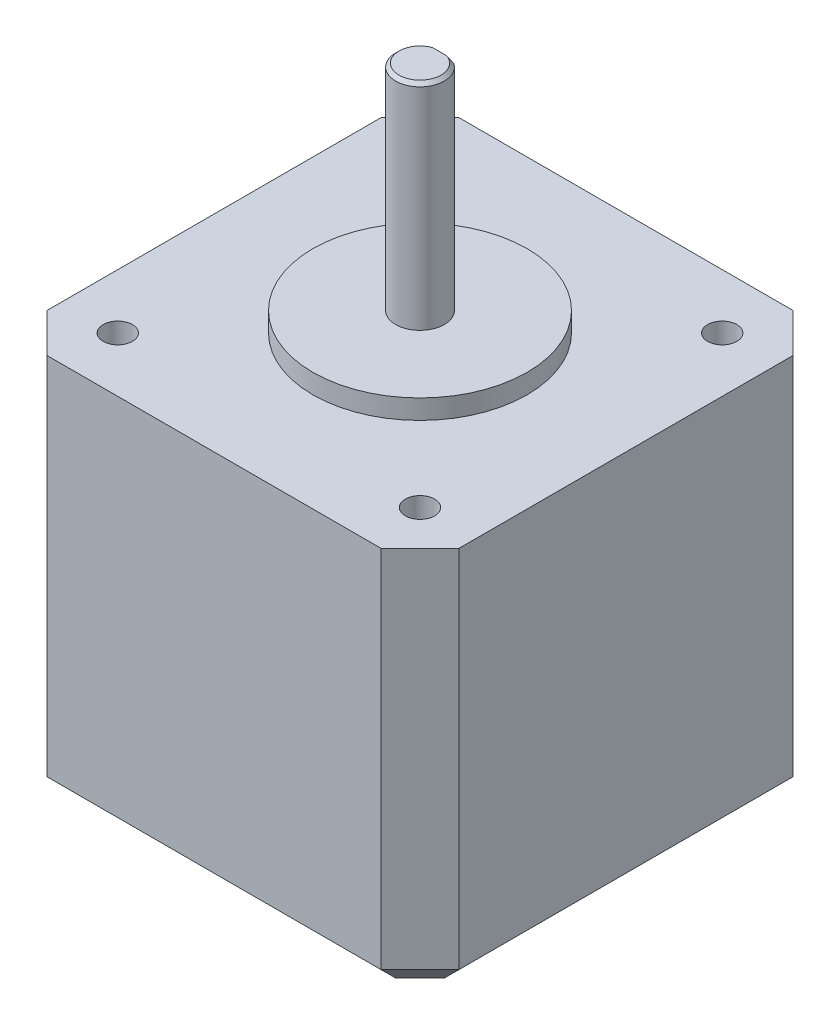
SolidWorks part; units mm, degrees
material "AISI Type A2 Tool Steel"
ref_plane "Front Plane" through (0, 0, 0) normal (0, 0, 1) x (1, 0, 0)
ref_plane "Top Plane" through (0, 0, 0) normal (0, 1, 0) x (1, 0, 0)
ref_plane "Right Plane" through (0, 0, 0) normal (1, 0, 0) x (0, 0, -1)
sketch "Sketch1" plane through (0, 0, 0) normal (0, 1, 0) x (1, 0, 0)
  line L0 (0, 42.3) -> (0, 0) construction
  line L1 (0, 0) -> (42.3, 0) construction
  line L2 (42.3, 0) -> (42.3, 42.3) construction
  line L3 (42.3, 42.3) -> (0, 42.3) construction
  line L4 (4, 42.3) -> (0, 38.3)
  line L5 (0, 38.3) -> (0, 4)
  line L6 (0, 4) -> (4, 0)
  line L7 (4, 0) -> (38.3, 0)
  line L8 (38.3, 0) -> (42.3, 4)
  line L9 (42.3, 4) -> (42.3, 38.3)
  line L10 (42.3, 38.3) -> (38.3, 42.3)
  line L11 (38.3, 42.3) -> (4, 42.3)
  line L12 (4, 42.3) -> (4, 0) construction
  line L13 (38.3, 0) -> (38.3, 42.3) construction
  line L14 (42.3, 38.3) -> (0, 38.3) construction
  line L15 (0, 4) -> (42.3, 4) construction
  line L16 (0, 42.3) -> (42.3, 0) construction
  line L17 (21.15, 21.15) -> (50021.15, 21.15) construction
  line L18 (21.15, 21.15) -> (21.15, -49978.85) construction
  point P6 (21.15, 21.15)
  dimension "D1" = 42.3
  dimension "D2" = 4
  dimension "D3" = 4
extrude "Boss-Extrude1" add sketch "Sketch1" along normal blind 40
sketch "Sketch2" plane through (0, 40, 0) normal (0, -1, 0) x (1, 0, 0)
  line L0 (0, -4) -> (0, 0) construction
  line L1 (0, 0) -> (4, 0) construction
  line L2 (38.3, -42.3) -> (42.3, -42.3) construction
  line L3 (42.3, -42.3) -> (42.3, -38.3) construction
  line L4 (0, 0) -> (42.3, -42.3) construction
  line L5 (21.15, -21.15) -> (50021.15, -21.15) construction
  line L6 (21.15, -21.15) -> (21.15, -50021.15) construction
  circle A0 centre (5.635, -5.635) radius 1.5
  circle A1 centre (36.665, -5.635) radius 1.5
  circle A2 centre (36.665, -36.665) radius 1.5
  circle A3 centre (5.635, -36.665) radius 1.5
  point P9 (21.15, -21.15)
  dimension "D1" = 3
  dimension "D2" = 15.515
  dimension "D3" = 15.515
extrude "Cut-Extrude1" cut sketch "Sketch2" along normal blind 5
sketch "Sketch5" plane through (0, 40, 0) normal (0, 1, 0) x (1, 0, 0)
  line L0 (5.635, 36.665) -> (36.665, 5.635) construction
  point P4 (21.15, 21.15)
ref_plane "Plane1" through (0, 0, -21.15) normal (0, 0, 1) x (1, 0, 0)
sketch "Sketch6" plane through (0, 0, -21.15) normal (0, 0, 1) x (1, 0, 0)
  line L0 (0, 40) -> (42.3, 40) construction
  line L1 (21.15, 40) -> (21.15, -49960) construction
  line L2 (21.15, 40) -> (32.15, 40)
  line L3 (32.15, 40) -> (32.15, 42)
  line L4 (32.15, 42) -> (23.65, 42)
  line L5 (23.65, 42) -> (23.65, 64)
  line L6 (23.65, 64) -> (21.15, 64)
  line L7 (21.15, 64) -> (21.15, 40)
  point P6 (21.15, 40)
  dimension "D1" = 11
  dimension "D2" = 2.5
  dimension "D3" = 2
  dimension "D4" = 24
revolve "Revolve1" add sketch "Sketch6" angle 360 about L7
chamfer "Chamfer1" distance 0.35 angle 45 1 edges at (18.65, 64, -21.15)
sketch "Sketch7" plane through (0, 64, 0) normal (0, 1, 0) x (1, 0, 0)
  line L0 (22.6213, 23.1712) -> (19.6787, 23.1712)
  circle A0 centre (21.15, 21.15) radius 2.5 construction
  arc A1 (22.6213, 23.1712) -> (19.6787, 23.1712) centre (21.15, 21.15) ccw
  point P5 (21.15, 18.65)
  dimension "D1" = 4.5212
extrude "D shaft" cut sketch "Sketch7" against normal up to surface (22 mm away) up to face at (18.65, 42, -21.15)
chamfer "Chamfer2" distance 2.54 angle 45 8 edges at (2, 0, -40.3) (0, 0, -21.15) (2, 0, -2) (21.15, 0, 0) (40.3, 0, -2) (42.3, 0, -21.15) (40.3, 0, -40.3) (21.15, 0, -42.3)
